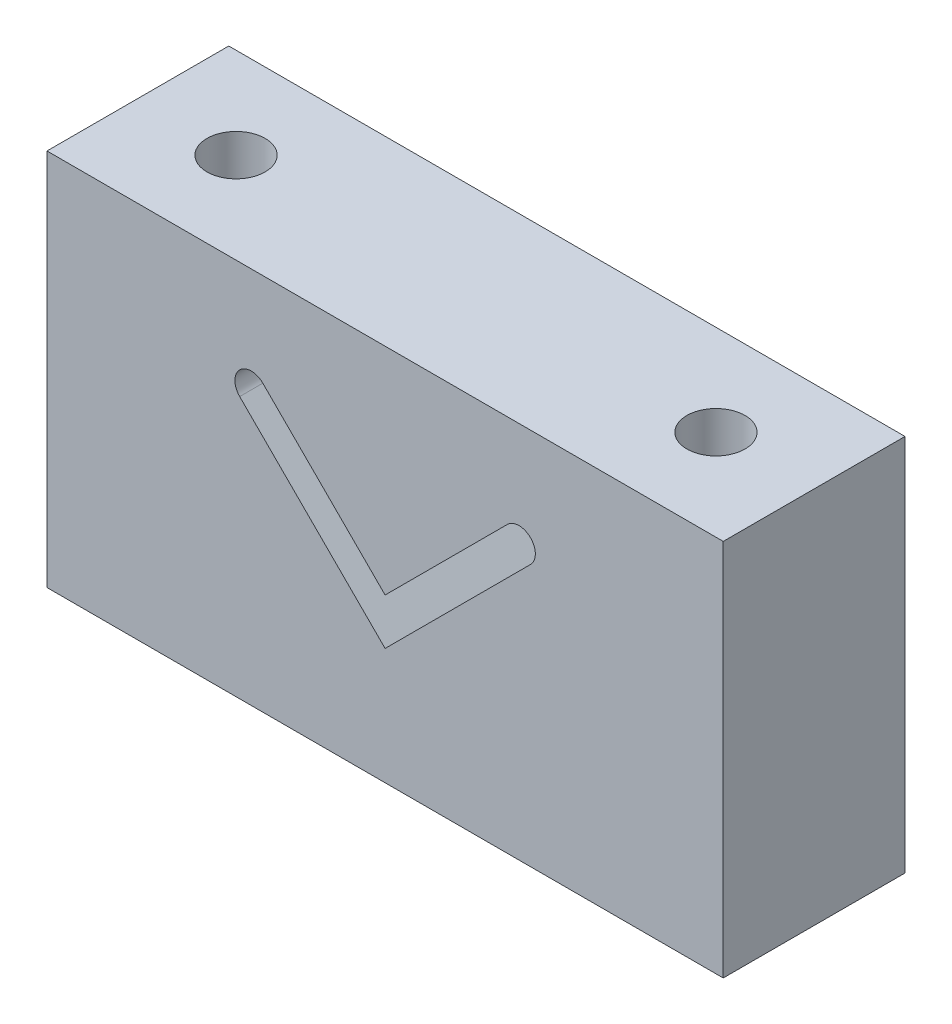
SolidWorks part; units mm, degrees
ref_plane "Front Plane" through (0, 0, 0) normal (0, 0, 1) x (1, 0, 0)
ref_plane "Top Plane" through (0, 0, 0) normal (0, 1, 0) x (1, 0, 0)
ref_plane "Right Plane" through (0, 0, 0) normal (1, 0, 0) x (0, 0, -1)
sketch "Sketch1" plane through (0, 0, 0) normal (0, 0, 1) x (1, 0, 0)
  line L1 (46.5, -26) -> (-46.5, -26)
  line L2 (46.5, -26) -> (46.5, 26)
  line L3 (46.5, 26) -> (-46.5, 26)
  line L4 (-46.5, -26) -> (-46.5, 26)
  line L5 (46.5, -26) -> (-46.5, 26) construction
  line L6 (46.5, 26) -> (-46.5, -26) construction
  point P0 (0, 0)
  dimension "D1" = 93
  dimension "D2" = 52
extrude "Boss-Extrude1" add sketch "Sketch1" along normal blind 25
sketch "Sketch2" plane through (0, 0, 0) normal (0, 0, -1) x (-1, 0, 0)
  line L0 (0, 0) -> (0, 50000) construction
  line L1 (0, -10) -> (20, 10)
  line L2 (0, 0) -> (-50000, 0) construction
  line L3 (0, -10) -> (-20, 10)
  line L4 (0, -3.636) -> (16.818, 13.182)
  line L5 (0, -3.636) -> (-16.818, 13.182)
  arc A0 (-20, 10) -> (-16.818, 13.182) centre (-18.409, 11.591) cw
  arc A1 (20, 10) -> (16.818, 13.182) centre (18.409, 11.591) ccw
  dimension "D1" = 10
  dimension "D2" = 45
  dimension "D3" = 10
  dimension "D4" = 4.5
extrude "Cut-Extrude1" cut sketch "Sketch2" against normal through all
sketch "Sketch3" plane through (0, -26, 0) normal (0, -1, 0) x (1, 0, 0)
  line L0 (0, 0) -> (0, 50000) construction
  line L1 (0, 0) -> (-50000, 0) construction
  circle A0 centre (-33, 12.5) radius 4
  circle A1 centre (33, 12.5) radius 4
  dimension "D2" = 8
  dimension "D1" = 33
  dimension "D3" = 12.5
extrude "Cut-Extrude2" cut sketch "Sketch3" against normal through all
